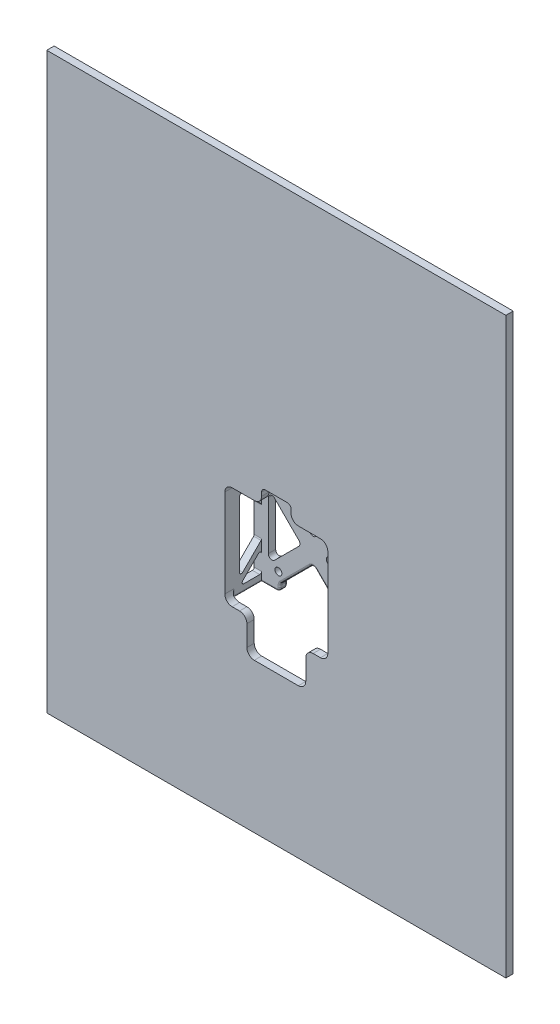
SolidWorks part; units mm, degrees
ref_plane "Front Plane" through (0, 0, 0) normal (0, 0, 1) x (1, 0, 0)
ref_plane "Top Plane" through (0, 0, 0) normal (0, 1, 0) x (1, 0, 0)
ref_plane "Right Plane" through (0, 0, 0) normal (1, 0, 0) x (0, 0, -1)
sketch "Sketch1" plane through (0, 0, 0) normal (0, 0, 1) x (1, 0, 0)
  line L1 (-99.06, -123.825) -> (99.06, -123.825)
  line L2 (-99.06, -123.825) -> (-99.06, 123.825)
  line L3 (-99.06, 123.825) -> (99.06, 123.825)
  line L4 (99.06, -123.825) -> (99.06, 123.825)
  line L5 (-99.06, -123.825) -> (99.06, 123.825) construction
  line L6 (-99.06, 123.825) -> (99.06, -123.825) construction
  line L7 (-22.225, -44.1325) -> (22.225, -44.1325)
  line L8 (-22.225, -44.1325) -> (-22.225, 0.3175)
  line L9 (-22.225, 0.3175) -> (22.225, 0.3175)
  line L10 (22.225, -44.1325) -> (22.225, 0.3175)
  line L11 (-22.225, -44.1325) -> (22.225, 0.3175) construction
  line L12 (-22.225, 0.3175) -> (22.225, -44.1325) construction
  point P0 (0, 0)
  point P6 (0, -21.9075)
  dimension "D1" = 198.12
  dimension "D2" = 247.65
  dimension "D3" = 44.45
  dimension "D4" = 79.6925
extrude "Boss-Extrude1" add sketch "Sketch1" along normal blind 3.175
fillet "Fillet1" radius 3.175 4 edges at (22.225, -44.1325, 1.5875) (22.225, 0.3175, 1.5875) (-22.225, 0.3175, 1.5875) (-22.225, -44.1325, 1.5875)
sketch "Sketch2" plane through (0, 0, 0) normal (0, 0, -1) x (-1, 0, 0)
  line L0 (22.225, -2.8575) -> (22.225, -40.9575) construction
  line L1 (19.05, -44.1325) -> (-19.05, -44.1325) construction
  line L2 (-22.225, -40.9575) -> (-22.225, -2.8575) construction
  line L3 (-19.05, 0.3175) -> (19.05, 0.3175) construction
  line L4 (-99.06, 123.825) -> (-99.06, -123.825)
  line L5 (-99.06, -123.825) -> (99.06, -123.825)
  line L6 (99.06, -123.825) -> (99.06, 123.825)
  line L7 (99.06, 123.825) -> (-99.06, 123.825)
  line L8 (-99.06, 123.825) -> (-99.06, -123.825)
  line L9 (-99.06, -123.825) -> (99.06, -123.825)
  line L10 (99.06, -123.825) -> (99.06, 123.825)
  line L11 (99.06, 123.825) -> (-99.06, 123.825)
  line L12 (22.225, -2.8575) -> (22.225, -40.9575)
  line L13 (19.05, -44.1325) -> (-19.05, -44.1325)
  line L14 (-22.225, -40.9575) -> (-22.225, -2.8575)
  line L15 (-19.05, 0.3175) -> (19.05, 0.3175)
  line L16 (-22.225, -21.9075) -> (-25.4, -21.9075)
  line L17 (22.225, -21.9075) -> (25.4, -21.9075)
  line L18 (-25.4, -44.4075) -> (-25.4, 0.5925)
  line L19 (25.4, -44.4075) -> (25.4, 0.5925)
  line L20 (-25.4, 0.5925) -> (-22.225, 0.5925)
  line L21 (-22.225, 0.5925) -> (-22.225, -2.8575)
  line L22 (-25.4, -44.4075) -> (-22.225, -44.4075)
  line L23 (-22.225, -44.4075) -> (-22.225, -40.9575)
  line L24 (25.4, 0.5925) -> (22.225, 0.5925)
  line L25 (22.225, 0.5925) -> (22.225, -2.8575)
  line L26 (25.4, -44.4075) -> (22.225, -44.4075)
  line L27 (22.225, -44.4075) -> (22.225, -40.9575)
  arc A1 (-22.225, -40.9575) -> (-19.05, -44.1325) centre (-19.05, -40.9575) ccw construction
  arc A2 (19.05, -44.1325) -> (22.225, -40.9575) centre (19.05, -40.9575) ccw construction
  arc A3 (22.225, -2.8575) -> (19.05, 0.3175) centre (19.05, -2.8575) ccw construction
  arc A4 (-19.05, 0.3175) -> (-22.225, -2.8575) centre (-19.05, -2.8575) ccw construction
  arc A5 (-22.225, -40.9575) -> (-19.05, -44.1325) centre (-19.05, -40.9575) ccw
  arc A6 (19.05, -44.1325) -> (22.225, -40.9575) centre (19.05, -40.9575) ccw
  arc A7 (22.225, -2.8575) -> (19.05, 0.3175) centre (19.05, -2.8575) ccw
  arc A8 (-19.05, 0.3175) -> (-22.225, -2.8575) centre (-19.05, -2.8575) ccw
  point P13 (-22.225, -21.9075)
  point P24 (-25.4, -21.9075)
  point P26 (22.225, -21.9075)
  point P27 (0, -21.9075)
  point P29 (25.4, -21.9075)
  point P64 (0, -16.8275)
  line M10 (22.225, -2.8575) -> (22.225, -40.9575)
  line M14 (-22.225, -40.9575) -> (-22.225, -2.8575)
  dimension "D2" = 3.175
  dimension "D3" = 45
  dimension "D1" = 0
ref_plane "Plane1" through (0, 0, -12.7) normal (0, 0, -1) x (-1, 0, 0)
sketch "Sketch4" plane through (0, 0, -12.7) normal (0, 0, -1) x (-1, 0, 0)
  line L0 (22.225, -2.8575) -> (22.225, -40.9575) construction
  line L1 (19.05, -44.1325) -> (-19.05, -44.1325) construction
  line L2 (-22.225, -40.9575) -> (-22.225, -2.8575) construction
  line L3 (-19.05, 0.3175) -> (19.05, 0.3175) construction
  line L4 (-99.06, 123.825) -> (-99.06, -123.825)
  line L5 (-99.06, -123.825) -> (99.06, -123.825)
  line L6 (99.06, -123.825) -> (99.06, 123.825)
  line L7 (99.06, 123.825) -> (-99.06, 123.825)
  line L8 (-99.06, 123.825) -> (-99.06, -123.825)
  line L9 (-99.06, -123.825) -> (99.06, -123.825)
  line L10 (99.06, -123.825) -> (99.06, 123.825)
  line L11 (99.06, 123.825) -> (-99.06, 123.825)
  line L12 (22.225, -2.8575) -> (22.225, -40.9575)
  line L13 (19.05, -44.1325) -> (-19.05, -44.1325)
  line L14 (-22.225, -40.9575) -> (-22.225, -2.8575)
  line L15 (-19.05, 0.3175) -> (19.05, 0.3175)
  line L16 (0, -16.87) -> (14.2875, -2.5825)
  line L17 (-22.5, -44.4075) -> (22.5, -44.4075)
  line L18 (-22.5, -44.4075) -> (-22.5, 0.5925)
  line L19 (-22.5, 0.5925) -> (22.5, 0.5925)
  line L20 (22.5, -44.4075) -> (22.5, 0.5925)
  line L21 (-22.5, -44.4075) -> (22.5, 0.5925) construction
  line L22 (-22.5, 0.5925) -> (22.5, -44.4075) construction
  line L23 (-19, -40.9075) -> (19, -40.9075)
  line L24 (-19, -40.9075) -> (-19, -2.9075)
  line L25 (-19, -2.9075) -> (19, -2.9075)
  line L26 (19, -40.9075) -> (19, -2.9075)
  line L27 (-19, -40.9075) -> (19, -2.9075) construction
  line L28 (-19, -2.9075) -> (19, -40.9075) construction
  line L29 (14.2875, -2.5825) -> (-14.2875, -2.5825)
  line L30 (-14.2875, -2.5825) -> (0, -16.87)
  line L40 (19.325, -7.62) -> (5.0375, -21.9075)
  line L41 (5.0375, -21.9075) -> (19.325, -36.195)
  line L42 (19.325, -36.195) -> (19.325, -7.62)
  line L43 (14.2875, -41.2325) -> (0, -26.945)
  line L44 (0, -26.945) -> (-14.2875, -41.2325)
  line L46 (-19.325, -36.195) -> (-5.0375, -21.9075)
  line L47 (-5.0375, -21.9075) -> (-19.325, -7.62)
  line L48 (-19.325, -7.62) -> (-19.325, -36.195)
  line L49 (-14.2875, -41.2325) -> (-14.2875, -44.4075)
  line L50 (14.2875, -41.2325) -> (14.2875, -44.4075)
  line L51 (-14.2875, -44.4075) -> (14.2875, -44.4075)
  line L53 (-14.2875, -41.2325) -> (14.2875, -41.2325) [skipped]
  circle A0 centre (-15, -6.9075) radius 1.5
  circle A1 centre (15, -6.9075) radius 1.5
  circle A2 centre (15, -36.9075) radius 1.5
  circle A3 centre (-15, -36.9075) radius 1.5
  point P12 (0, 0.3175)
  point P13 (22.225, -21.9075)
  point P14 (0, -21.9075)
  point P20 (0, -21.9075)
  point P32 (0, -16.87)
  point P48 (2.54, -19.3675)
  point P49 (0, -21.9075)
  dimension "D4" = 3
  dimension "D2" = 45
  dimension "D3" = 38
  dimension "D5" = 4
  dimension "D6" = 45
  dimension "D7" = 28.575
  dimension "D8" = 3.175
  dimension "D9" = 4
  dimension "D1" = 0
extrude "Boss-Extrude3" add sketch "Sketch4" along normal blind 3.175 separate body
extrude "Boss-Extrude4" add sketch "Sketch2" along normal up to surface (15.875 mm away) contours L21 L20 L18 L16 L14 | L22 L23 L16 L18 M14 | L27 L26 L19 L17 L12 | L24 L25 L17 L19 M10 up to face at (0, -31.7617, -15.875)
sketch "Sketch6" plane through (25.4, 0, 0) normal (1, 0, 0) x (0, 0, -1)
  line L14 (0, -44.4075) -> (15.875, -44.4075)
  line L15 (15.875, -44.4075) -> (15.875, 0.5925)
  line L16 (15.875, 0.5925) -> (0, 0.5925)
  line L17 (0, 0.5925) -> (0, -44.4075)
  line L18 (0, -44.4075) -> (15.875, -44.4075)
  line L19 (15.875, -44.4075) -> (15.875, 0.5925)
  line L20 (15.875, 0.5925) -> (0, 0.5925)
  line L21 (0, 0.5925) -> (0, -44.4075)
  line L51 (12.7, -21.9075) -> (3.175, -21.9075)
  line L52 (3.175, -2.5825) -> (12.7, -2.5825)
  line L53 (3.175, -2.5825) -> (3.175, -41.2325)
  line L54 (3.175, -41.2325) -> (12.7, -41.2325)
  line L55 (12.7, -2.5825) -> (12.7, -41.2325)
  line L61 (3.175, -41.2325) -> (3.175, -38.0575)
  line L62 (3.175, -38.0575) -> (12.7, -28.5325)
  line L63 (12.7, -28.5325) -> (12.7, -31.7075)
  line L64 (12.7, -31.7075) -> (3.175, -41.2325)
  line L65 (12.7, -15.2825) -> (12.7, -12.1075)
  line L66 (3.175, -5.7575) -> (12.7, -15.2825)
  line L67 (3.175, -2.5825) -> (3.175, -5.7575)
  line L68 (12.7, -12.1075) -> (3.175, -2.5825)
  point P0 (12.7, -41.2325)
  point P12 (3.175, -2.5825)
  point P14 (12.7, -21.9075)
  point P20 (0, 0)
  dimension "D4" = 3.175
  dimension "D5" = 3.175
  dimension "D7" = 3.175
  dimension "D8" = 3.175
  dimension "D9" = 135
  dimension "D10" = 135
  dimension "D11" = 3.175
  dimension "D1" = 0
fillet "Fillet2" radius 1.5875 14 edges at (19.325, -36.195, -14.2875) (-5.0375, -21.9075, -14.2875) (19.325, -7.62, -14.2875) (0, -26.945, -14.2875) (-19.325, -7.62, -14.2875) (-19.325, -36.195, -14.2875) (0, -16.87, -14.2875) (-14.2875, -2.5825, -14.2875) (14.2875, -2.5825, -14.2875) (5.0375, -21.9075, -14.2875) (-14.2875, -44.4075, -14.2875) (-14.2875, -41.2325, -14.2875) (14.2875, -44.4075, -14.2875) (14.2875, -41.2325, -14.2875)
fillet "Fillet5" radius 0.7937 40 edges at (22.225, -1.1325, 0) (-22.225, -1.1325, 0) (25.4, -21.9075, 0) (-25.4, -21.9075, 0) (-22.225, -42.6825, 0) (25.4, 0.5925, -7.9375) (23.8125, 0.5925, 0) (22.225, 0.5925, -6.35) (0, 0.5925, -12.7) (-22.225, 0.5925, -6.35) (-23.8125, 0.5925, 0) (-25.4, 0.5925, -7.9375) (0, 0.5925, -15.875) (20.6375, -44.4075, -15.875) (-20.6375, -44.4075, -15.875) (-23.8125, -44.4075, 0) (19.05, -44.4075, -12.7) (-19.05, -44.4075, -12.7) (-25.4, -21.9075, -15.875) (25.4, -21.9075, -15.875) (-25.4, -44.4075, -7.9375) (-22.225, -44.4075, -6.35) (14.7525, -43.9425, -15.875) (14.7525, -43.9425, -12.7) (14.2875, -42.355, -15.875) (14.2875, -42.355, -12.7) (14.1667, -41.2826, -15.875) (14.1667, -41.2826, -12.7) (7.4725, -34.4175, -15.875) (7.4725, -34.4175, -12.7) (0, -27.6026, -15.875) (0, -27.6026, -12.7) (-7.4725, -34.4175, -12.7) (-7.4725, -34.4175, -15.875) (-14.1667, -41.2826, -15.875) (-14.1667, -41.2826, -12.7) (-14.2875, -42.355, -12.7) (-14.2875, -42.355, -15.875) (-14.7525, -43.9425, -15.875) (-14.7525, -43.9425, -12.7)
extrude "Cut-Extrude1" cut sketch "Sketch6" against normal up to surface (50.8 mm away) contours L68 L55 L52 | L66 L53 L51 L55 | L53 L62 L55 L51 | L55 L64 L54 up to face at (-25.4, -21.9075, -7.9375)
fillet "Fillet6" radius 0.7937 20 edges at (23.8125, -15.2825, -12.7) (23.8125, -28.5325, -12.7) (-23.8125, -15.2825, -12.7) (-23.8125, -28.5325, -12.7) (23.8125, -12.1075, -12.7) (23.8125, -2.5825, -12.7) (23.8125, -2.5825, -3.175) (-23.8125, -12.1075, -12.7) (-23.8125, -2.5825, -12.7) (-23.8125, -31.7075, -12.7) (-23.8125, -41.2325, -12.7) (-23.8125, -38.0575, -3.175) (-23.8125, -41.2325, -3.175) (-23.8125, -2.5825, -3.175) (-23.8125, -5.7575, -3.175) (23.8125, -5.7575, -3.175) (23.8125, -38.0575, -3.175) (23.8125, -41.2325, -12.7) (23.8125, -31.7075, -12.7) (23.8125, -41.2325, -3.175)
sketch "Sketch8" plane through (0, 0, 0) normal (0, 0, -1) x (-1, 0, 0)
  line L0 (19.05, -44.1325) -> (-19.05, -44.1325) construction
  line L1 (-19.05, 0.3175) -> (19.05, 0.3175) construction
  line L2 (12.7, -28.8925) -> (-12.7, -28.8925)
  line L3 (12.7, -28.8925) -> (12.7, -59.3725)
  line L4 (-99.06, 123.825) -> (-99.06, -123.825)
  line L5 (-99.06, -123.825) -> (99.06, -123.825)
  line L6 (99.06, -123.825) -> (99.06, 123.825)
  line L7 (99.06, 123.825) -> (-99.06, 123.825)
  line L8 (-99.06, 123.825) -> (-99.06, -123.825)
  line L9 (-99.06, -123.825) -> (99.06, -123.825)
  line L10 (99.06, -123.825) -> (99.06, 123.825)
  line L11 (99.06, 123.825) -> (-99.06, 123.825)
  line L12 (12.7, -59.3725) -> (-12.7, -59.3725)
  line L13 (-12.7, -28.8925) -> (-12.7, -59.3725)
  line L14 (12.7, -28.8925) -> (-12.7, -59.3725) construction
  line L15 (12.7, -59.3725) -> (-12.7, -28.8925) construction
  line L17 (6.35, 6.6675) -> (-6.35, 6.6675)
  line L18 (6.35, 6.6675) -> (6.35, -6.0325)
  line L19 (6.35, -6.0325) -> (-6.35, -6.0325)
  line L20 (-6.35, 6.6675) -> (-6.35, -6.0325)
  line L21 (6.35, 6.6675) -> (-6.35, -6.0325) construction
  line L22 (6.35, -6.0325) -> (-6.35, 6.6675) construction
  point P2 (0, -44.1325)
  point P4 (0, -44.1325)
  point P12 (0, 0.3175)
  point P13 (0, 0.3175)
  line M20 (-19.05, 0.3175) -> (19.05, 0.3175)
  line M32 (19.05, -44.1325) -> (-19.05, -44.1325)
  dimension "D2" = 25.4
  dimension "D3" = 15.24
  dimension "D4" = 12.7
  dimension "D5" = 6.35
  dimension "D1" = 0
extrude "Cut-Extrude2" cut sketch "Sketch8" against normal up to next contours L13 L12 L3 M32 | L17 L20 L18 M20
fillet "Fillet7" radius 3.175 6 edges at (-6.35, 0.3175, 1.5875) (6.35, 0.3175, 1.5875) (-12.7, -44.1325, 1.5875) (12.7, -44.1325, 1.5875) (12.7, -59.3725, 1.5875) (-12.7, -59.3725, 1.5875)
fillet "Fillet9" radius 1.5875 2 edges at (-6.35, 6.6675, 1.5875) (6.35, 6.6675, 1.5875)
